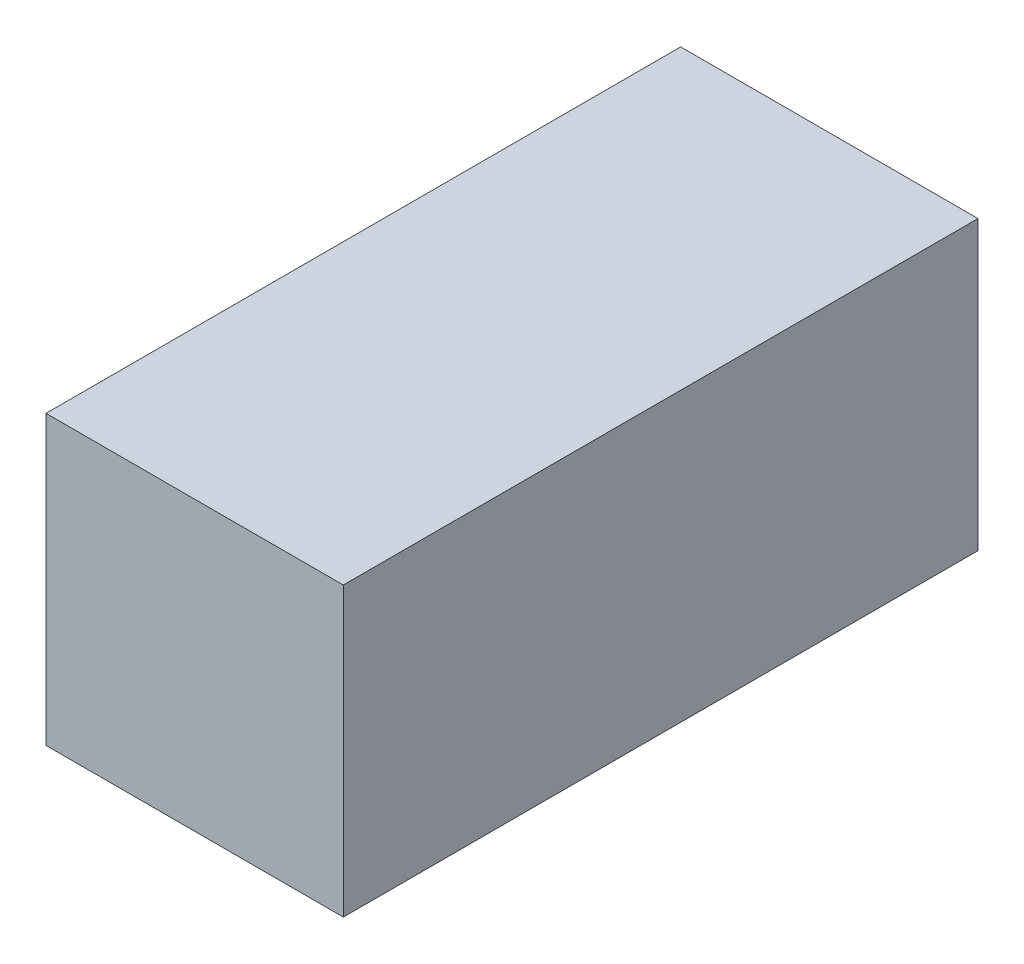
SolidWorks part; units mm, degrees
ref_plane "Front Plane" through (0, 0, 0) normal (0, 0, 1) x (1, 0, 0)
ref_plane "Top Plane" through (0, 0, 0) normal (0, 1, 0) x (1, 0, 0)
ref_plane "Right Plane" through (0, 0, 0) normal (1, 0, 0) x (0, 0, -1)
sketch "Sketch2" plane through (0, 0, 0) normal (0, 0, 1) x (1, 0, 0)
  line L0 (-12.25, -11.85) -> (12.25, 11.85) construction
  line L1 (-12.25, 11.85) -> (12.25, 11.85)
  line L2 (-12.25, 11.85) -> (-12.25, -11.85)
  line L3 (-12.25, -11.85) -> (12.25, -11.85)
  line L4 (12.25, 11.85) -> (12.25, -11.85)
  point P4 (0, 0)
  dimension "D1" = 24.5
  dimension "D2" = 23.7
extrude "Extrude1" add sketch "Sketch2" along normal blind 52.3
